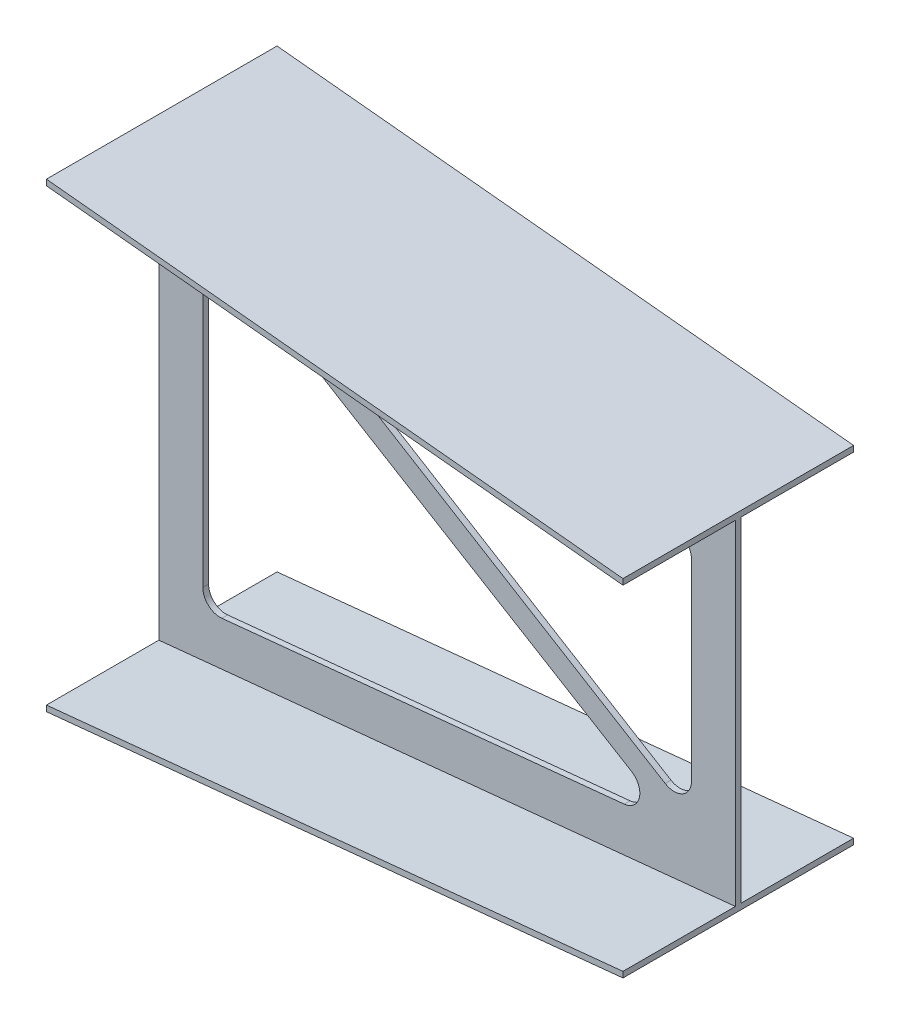
SolidWorks part; units mm, degrees
ref_plane "Front Plane" through (0, 0, 0) normal (0, 0, 1) x (1, 0, 0)
ref_plane "Top Plane" through (0, 0, 0) normal (0, 1, 0) x (1, 0, 0)
ref_plane "Right Plane" through (0, 0, 0) normal (1, 0, 0) x (0, 0, -1)
sketch "Sketch1" plane through (0, 0, 0) normal (1, 0, 0) x (0, 0, -1)
  line L1 (-205, 400) -> (195, 400)
  line L2 (-205, 400) -> (-205, 390)
  line L4 (195, 400) -> (195, 390)
  line L6 (-205, -390) -> (-205, -400)
  line L7 (-205, -400) -> (195, -400)
  line L8 (195, -390) -> (195, -400)
  line L15 (-205, -390) -> (-10, -390)
  line L16 (-5, 390) -> (-5, -590) construction
  line L18 (-205, 390) -> (-10, 390)
  line L19 (0, 0) -> (192.2403, 0) construction
  line L21 (-10, 390) -> (-10, -390)
  line L23 (0, 390) -> (0, -390)
  line L27 (0, 390) -> (195, 390)
  line L28 (0, -390) -> (195, -390)
  dimension "D1" = 400
  dimension "D2" = 10
  dimension "D3" = 800
  dimension "D4" = 10
ref_plane "Plane2" through (1000, 0, 0) normal (1, 0, 0) x (0, 0, -1)
sketch "Sketch4" plane through (1000, 0, -1000) normal (-1, 0, 0) x (0, 0, 1)
  line L1 (805, 300) -> (1205, 300)
  line L2 (805, 300) -> (805, 290)
  line L4 (1205, 300) -> (1205, 290)
  line L6 (805, -290) -> (805, -300)
  line L7 (805, -300) -> (1205, -300)
  line L8 (1205, -290) -> (1205, -300)
  line L15 (805, -290) -> (1000, -290)
  line L16 (1005, 390) -> (1005, -390) construction
  line L18 (805, 290) -> (1000, 290)
  line L19 (1010, -290) -> (1205, -290)
  line L21 (1000, 290) -> (1000, -290)
  line L23 (1010, 290) -> (1010, -290)
  line L24 (1010, 290) -> (1205, 290)
  line L26 (1010, 390) -> (1010, -390) construction
  line L27 (1000, 0) -> (820.2065, 0) construction
  dimension "D1" = 400
  dimension "D2" = 10
  dimension "D3" = 600
  dimension "D4" = 10
loft "Loft4" add profiles "Sketch1", "Sketch4"
sketch "Sketch6" plane through (0, 0, 10) normal (0, 0, 1) x (1, 0, 0)
  line L4 (221.7369, 233.9171) -> (878.1892, -166.097)
  line L5 (121.7277, 245.1095) -> (819.8042, -177.1738)
  line L8 (76.2, -305.7999) -> (923.8, -221.0399)
  line L9 (923.8, -221.0399) -> (923.8, 221.0399)
  line L10 (923.8, 221.0399) -> (76.2, 305.7999)
  line L11 (76.2, 305.7999) -> (76.2, -305.7999)
  line L16 (109.1851, -302.5014) -> (807.2616, -232.6938)
  line L17 (923.8, -140.4786) -> (923.8, 193.8903)
  line L18 (896.7851, 223.7414) -> (240.3328, 289.3867)
  line L19 (76.2, 219.4407) -> (76.2, -272.6503)
  arc A4 (923.8, 193.8903) -> (896.7851, 223.7414) centre (893.8, 193.8903) ccw
  arc A6 (109.1851, -302.5014) -> (76.2, -272.6503) centre (106.2, -272.6503) cw
  arc A8 (807.2616, -232.6938) -> (819.8042, -177.1738) centre (804.2765, -202.8427) ccw
  arc A9 (923.8, -140.4786) -> (878.1892, -166.097) centre (893.8, -140.4786) cw
  arc A10 (76.2, 219.4407) -> (121.7277, 245.1095) centre (106.2, 219.4407) cw
  arc A11 (221.7369, 233.9171) -> (240.3328, 289.3867) centre (237.3477, 259.5355) cw
  dimension "D2" = 30
  dimension "D3" = 30
  dimension "D1" = 76.2
extrude "Cut-Extrude1" cut sketch "Sketch6" against normal through all
